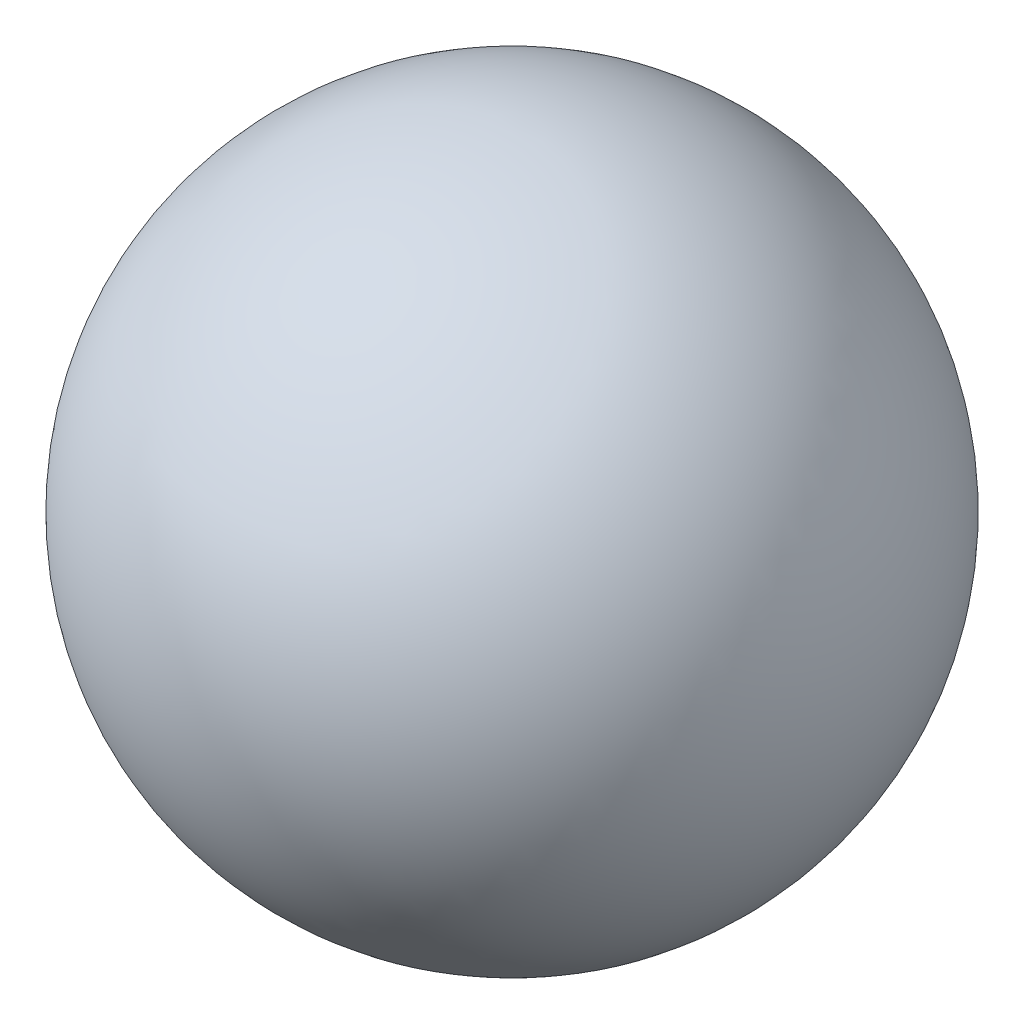
SolidWorks part; units mm, degrees
ref_plane "Front Plane" through (0, 0, 0) normal (0, 0, 1) x (1, 0, 0)
ref_plane "Top Plane" through (0, 0, 0) normal (0, 1, 0) x (1, 0, 0)
ref_plane "Right Plane" through (0, 0, 0) normal (1, 0, 0) x (0, 0, -1)
sketch "Sketch1" plane through (0, 0, 0) normal (0, 0, 1) x (1, 0, 0)
  line L0 (0, 1.25) -> (0, -1.25)
  arc A0 (0, -1.25) -> (0, 1.25) centre (0, 0) ccw
  dimension "D1" = 2.5
revolve "Revolve1" add sketch "Sketch1" angle 360 about L0
